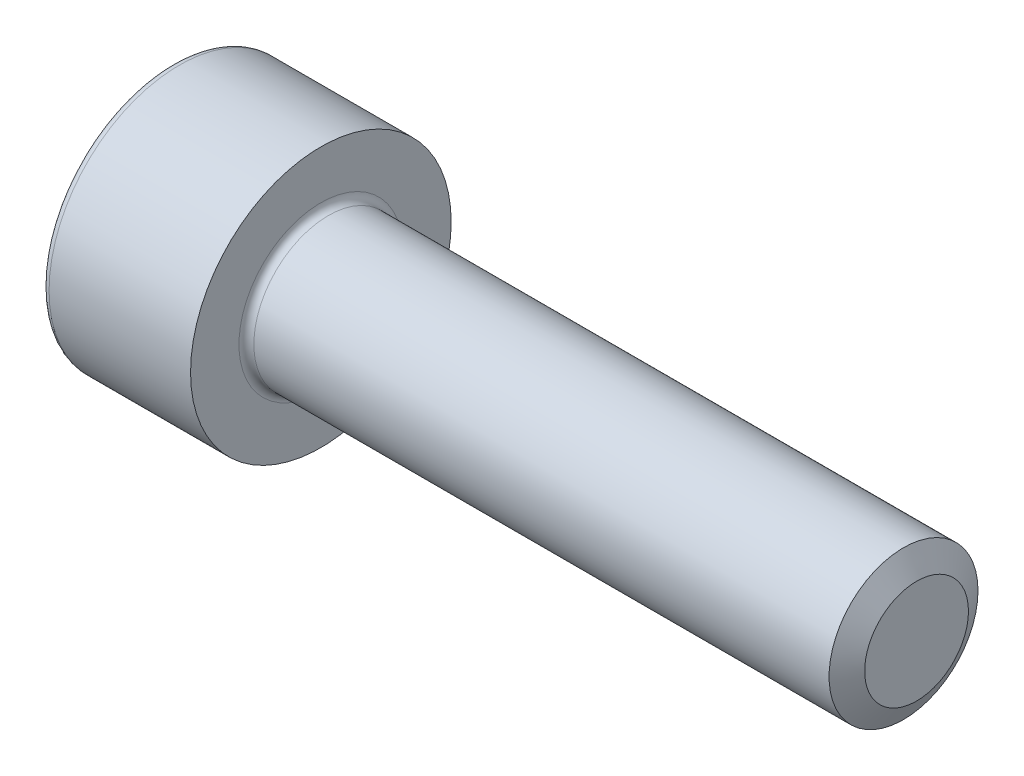
SolidWorks part; units mm, degrees
material "AISI 304"
ref_plane "前视基准面" through (0, 0, 0) normal (0, 0, 1) x (1, 0, 0)
ref_plane "上视基准面" through (0, 0, 0) normal (0, 1, 0) x (1, 0, 0)
ref_plane "右视基准面" through (0, 0, 0) normal (1, 0, 0) x (0, 0, -1)
sketch "草图1" plane through (0, 0, 0) normal (0, 0, 1) x (1, 0, 0)
  line L0 (0, 3.5) -> (0, 0)
  line L1 (0, 0) -> (4, 0)
  line L2 (4, 0) -> (4, 3.5)
  line L3 (4, 3.5) -> (0, 3.5)
  line L4 (0, 0) -> (4, 0) construction
revolve "旋转1" add sketch "草图1" angle 360 about L4
sketch "草图2" plane through (4, 0, 0) normal (1, 0, 0) x (0, 0, -1)
  circle A0 centre (0, 0) radius 2
extrude "凸台-拉伸1" add sketch "草图2" along normal blind 16
sketch "草图3" plane through (0, 0, 0) normal (-1, 0, 0) x (0, 0, 1)
  line L0 (0, 1.72) -> (-1.4896, 0.86)
  line L1 (-1.4896, 0.86) -> (-1.4896, -0.86)
  line L2 (-1.4896, -0.86) -> (0, -1.72)
  line L3 (0, -1.72) -> (1.4896, -0.86)
  line L4 (1.4896, -0.86) -> (1.4896, 0.86)
  line L5 (1.4896, 0.86) -> (0, 1.72)
extrude "切除-拉伸1" cut sketch "草图3" against normal blind 2
chamfer "倒角1" distance 0.6062 angle 30.001 1 edges at (20, 0, -2)
fillet "圆角1" radius 0.2 2 edges at (4, 0, -2) (0, 0, -3.5)
